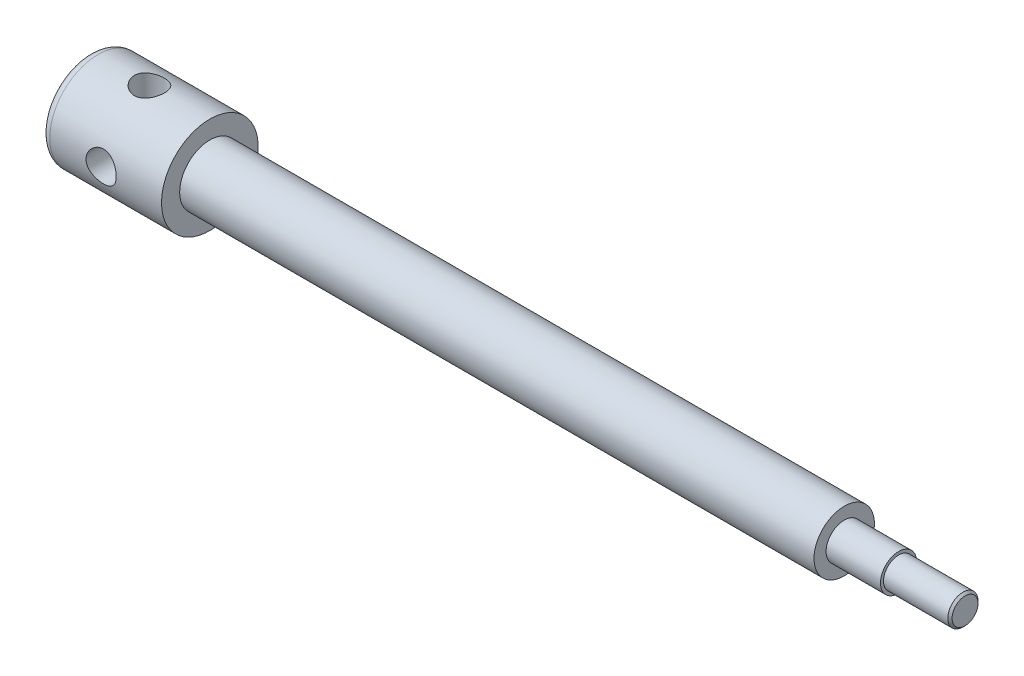
SolidWorks part; units mm, degrees
ref_plane "Front Plane" through (0, 0, 0) normal (0, 0, 1) x (1, 0, 0)
ref_plane "Top Plane" through (0, 0, 0) normal (0, 1, 0) x (1, 0, 0)
ref_plane "Right Plane" through (0, 0, 0) normal (1, 0, 0) x (0, 0, -1)
sketch "Sketch1" plane through (0, 0, 0) normal (0, 0, 1) x (1, 0, 0)
  line L0 (-31.9454, 0) -> (260.0155, 0) construction
  line L1 (238.0155, 6) -> (238.0155, 5)
  line L2 (238.0155, 6) -> (220.0155, 6)
  line L3 (220.0155, 6) -> (220.0155, 9.9984)
  line L4 (220.0155, 9.9984) -> (10.0155, 9.9984)
  line L5 (10.0155, 9.9984) -> (10.0155, 16)
  line L6 (10.0155, 16) -> (-26.9845, 16)
  line L7 (-29.9845, 13) -> (-29.9845, 0)
  line L8 (238.0155, 5) -> (259.3084, 5)
  line L9 (260.0155, 4.2929) -> (260.0155, 0)
  line L10 (260.0155, 0) -> (-29.9845, 0)
  line L11 (260.0155, 4.2929) -> (259.3084, 5)
  arc A0 (-26.9845, 16) -> (-29.9845, 13) centre (-26.9845, 13) ccw
  dimension "D9" = 3
  dimension "D2" = 6
  dimension "D3" = 22
  dimension "D4" = 18
  dimension "D5" = 250
  dimension "D6" = 40
  dimension "D7" = 16
  dimension "D8" = 9.9984
  dimension "D10" = 1
  dimension "D11" = 45
revolve "Revolve1" add sketch "Sketch1" angle 360 about L0
cosmetic thread "Cosmetic Thread1" parameters "D1"=170, "D2"=17.252
cosmetic thread "Cosmetic Thread2" parameters "D1"=22, "D2"=8.619
sketch "Sketch2" plane through (0, 0, 0) normal (0, 1, 0) x (1, 0, 0)
  line L0 (10.0155, -9.9984) -> (10.0155, 9.9984) construction
  line L1 (-26.9845, -16) -> (10.0155, -16) construction
  circle A0 centre (-9.9845, 0) radius 5
  dimension "D3" = 10
  dimension "D1" = 20
  dimension "D2" = 16
extrude "Cut-Extrude1" cut sketch "Sketch2" against normal mid plane 100
sketch "Sketch3" plane through (0, 0, 0) normal (0, 0, 1) x (1, 0, 0)
  line L0 (10.0155, -16) -> (10.0155, 16) construction
  circle A0 centre (-9.9845, 0) radius 5
  dimension "D2" = 10
  dimension "D1" = 20
extrude "Cut-Extrude2" cut sketch "Sketch3" against normal mid plane 100
sketch "Sketch4" plane through (0, 0, 0) normal (0, 0, 1) x (1, 0, 0)
  line L0 (50.0155, 9.9984) -> (50.0155, -9.9984)
  line L1 (220.0155, 9.9984) -> (10.0155, 9.9984) construction
  line L2 (10.0155, -9.9984) -> (220.0155, -9.9984) construction
  line L4 (220.0155, -6) -> (220.0155, 6) construction
  dimension "D1" = 170
